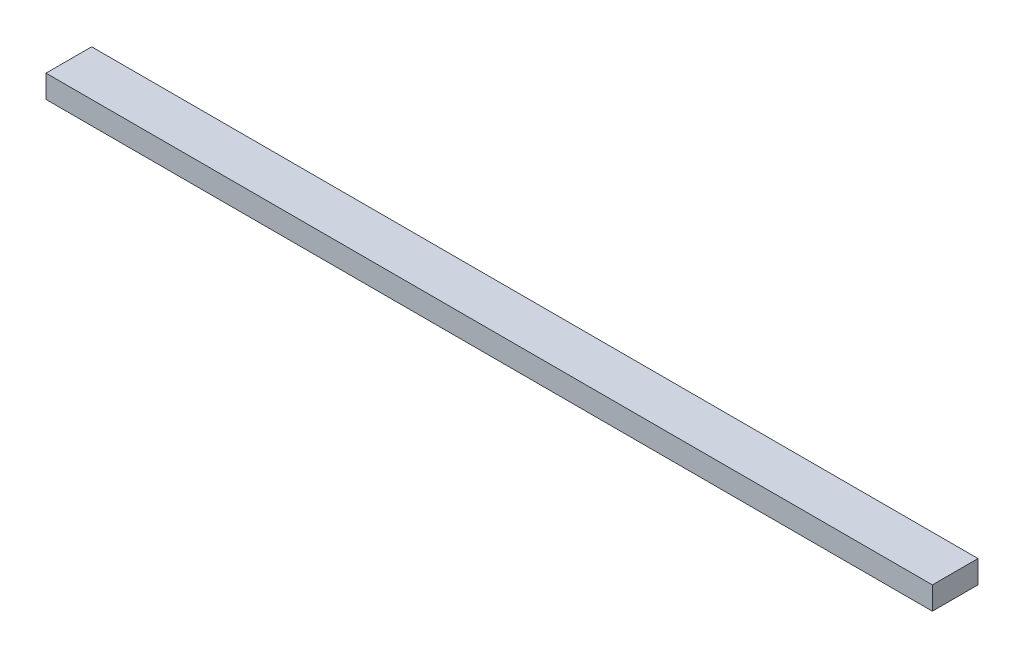
SolidWorks part; units mm, degrees
ref_plane "Front Plane" through (0, 0, 0) normal (0, 0, 1) x (1, 0, 0)
ref_plane "Top Plane" through (0, 0, 0) normal (0, 1, 0) x (1, 0, 0)
ref_plane "Right Plane" through (0, 0, 0) normal (1, 0, 0) x (0, 0, -1)
sketch "Sketch1" plane through (0, 0, 0) normal (1, 0, 0) x (0, 0, -1)
  line L1 (0, 0) -> (38.1, 0)
  line L2 (0, 0) -> (0, 19.05)
  line L3 (0, 19.05) -> (38.1, 19.05)
  line L4 (38.1, 0) -> (38.1, 19.05)
  dimension "D1" = 38.1
  dimension "D2" = 19.05
extrude "Boss-Extrude1" add sketch "Sketch1" along normal blind 740
